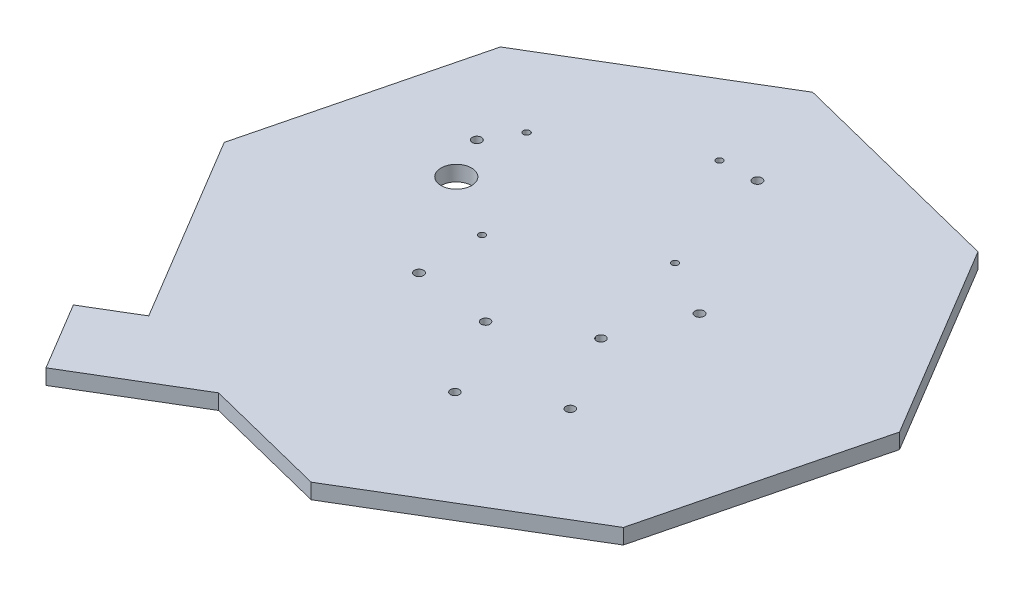
SolidWorks part; units mm, degrees
ref_plane "Front Plane" through (0, 0, 0) normal (0, 0, 1) x (1, 0, 0)
ref_plane "Top Plane" through (0, 0, 0) normal (0, 1, 0) x (1, 0, 0)
ref_plane "Right Plane" through (0, 0, 0) normal (1, 0, 0) x (0, 0, -1)
sketch "Sketch1" plane through (0, 0, 0) normal (0, 1, 0) x (1, 0, 0)
  line L1 (73.765, 99.3213) -> (-18.0711, 122.3905)
  line L2 (-18.0711, 122.3905) -> (-99.3213, 73.765)
  line L3 (-99.3213, 73.765) -> (-122.3905, -18.0711)
  line L4 (-122.3905, -18.0711) -> (-73.765, -99.3213)
  line L5 (-73.765, -99.3213) -> (18.0711, -122.3905)
  line L6 (18.0711, -122.3905) -> (99.3213, -73.765)
  line L7 (99.3213, -73.765) -> (122.3905, 18.0711)
  line L8 (122.3905, 18.0711) -> (73.765, 99.3213)
  circle A0 centre (0, 0) radius 114.3 construction
extrude "Boss-Extrude2" add sketch "Sketch1" along normal blind 6.35
sketch "Sketch2" plane through (0, 6.35, 0) normal (0, 1, 0) x (-1, 0, 0)
  line L0 (75.5911, 96.27) -> (95.2066, 108.0093)
  line L1 (122.3905, 18.0711) -> (73.765, 99.3213) construction
  line L2 (95.2066, 108.0093) -> (78.2499, 136.3429)
  line L3 (78.2499, 136.3429) -> (33.3521, 109.473)
  line L4 (73.765, 99.3213) -> (-18.0711, 122.3905) construction
  line L5 (73.765, 99.3213) -> (75.5911, 96.27)
  line L6 (73.765, 99.3213) -> (33.3521, 109.473)
  dimension "D1" = 22.86
  dimension "D2" = 3.556
  dimension "D3" = 33.02
extrude "Boss-Extrude3" add sketch "Sketch2" against normal blind 6.35
sketch "Sketch3" plane through (0, 0, 0) normal (0, -1, 0) x (1, 0, 0)
  line L28 (122.3905, -18.0711) -> (99.3213, 73.765)
  circle A0 centre (-63.0561, -48.3878) radius 1.3716 construction
  circle A1 centre (-35.4167, -2.2041) radius 1.3716 construction
  circle A2 centre (14.7948, -32.2539) radius 1.3716 construction
  circle A3 centre (-12.8446, -78.4376) radius 1.3716 construction
  circle A4 centre (-63.0561, -48.3878) radius 1.3716
  circle A5 centre (-35.4167, -2.2041) radius 1.3716
  circle A6 centre (14.7948, -32.2539) radius 1.3716
  circle A7 centre (-12.8446, -78.4376) radius 1.3716
extrude "Cut-Extrude1" cut sketch "Sketch3" against normal through all contours A7 | A5 | A4 | A6
sketch "Sketch4" plane through (0, 0, 0) normal (0, -1, 0) x (1, 0, 0)
  circle A0 centre (-61.7374, -17.8145) radius 6.35 construction
  circle A1 centre (-61.7374, -17.8145) radius 6.35
extrude "Cut-Extrude2" cut sketch "Sketch4" against normal through all
sketch "Sketch5" plane through (0, 0, 0) normal (0, -1, 0) x (1, 0, 0)
  circle A0 centre (2.2673, -79.0601) radius 1.905 construction
  circle A1 centre (-70.7462, -35.364) radius 1.905 construction
  circle A2 centre (38.1372, -19.1237) radius 1.905 construction
  circle A3 centre (-34.8763, 24.5724) radius 1.905 construction
  circle A4 centre (2.2673, -79.0601) radius 1.905
  circle A5 centre (-70.7462, -35.364) radius 1.905
  circle A6 centre (38.1372, -19.1237) radius 1.905
  circle A7 centre (-34.8763, 24.5724) radius 1.905
extrude "Cut-Extrude3" cut sketch "Sketch5" against normal through all
sketch "Sketch7" plane through (0, 6.35, 0) normal (0, 1, 0) x (1, 0, 0)
  circle A0 centre (15.5386, -60.0421) radius 1.85 construction
  circle A1 centre (-3.4619, -28.2934) radius 1.85 construction
  circle A2 centre (26.5707, -10.3199) radius 1.85 construction
  circle A3 centre (45.5712, -42.0686) radius 1.85 construction
  circle A4 centre (15.5386, -60.0421) radius 1.85
  circle A5 centre (-3.4619, -28.2934) radius 1.85
  circle A6 centre (26.5707, -10.3199) radius 1.85
  circle A7 centre (45.5712, -42.0686) radius 1.85
extrude "Cut-Extrude4" cut sketch "Sketch7" against normal through all
equation "\"baselength\"=9"
equation "\"material\"=\"GMaterial@Platform.assembly\""
equation "\"D1@Boss-Extrude2\" = \"material\""
equation "\"D1@Boss-Extrude3\" = \"material\""
